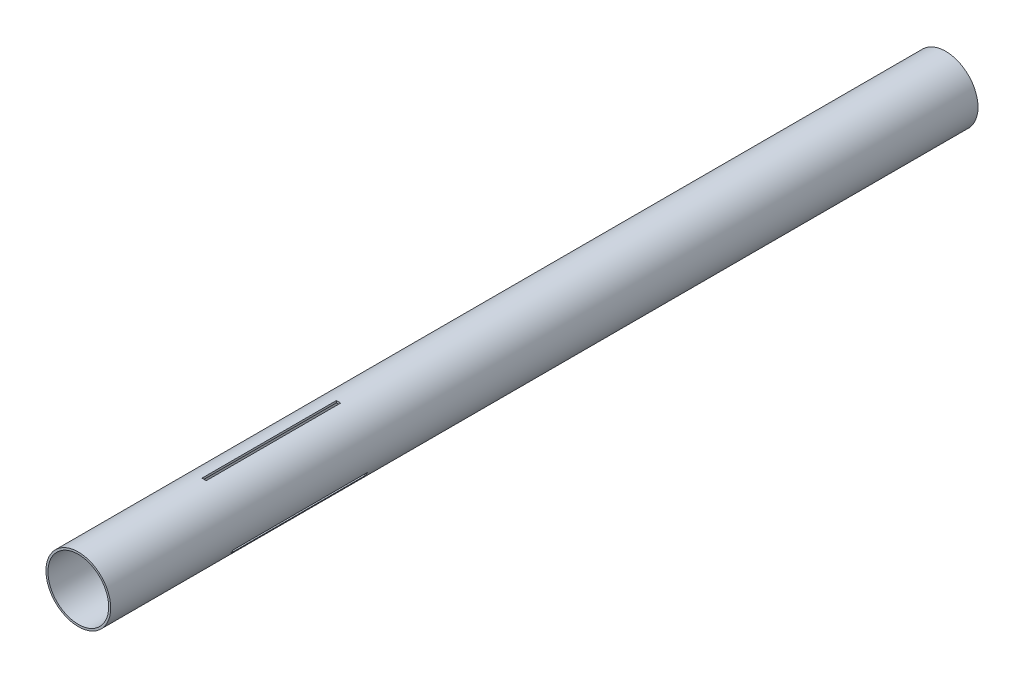
SolidWorks part; units mm, degrees
ref_plane "Front Plane" through (0, 0, 0) normal (0, 0, 1) x (1, 0, 0)
ref_plane "Top Plane" through (0, 0, 0) normal (0, 1, 0) x (1, 0, 0)
ref_plane "Right Plane" through (0, 0, 0) normal (1, 0, 0) x (0, 0, -1)
sketch "Sketch1" plane through (0, 0, 0) normal (0, 0, 1) x (1, 0, 0)
  circle A0 centre (0, 0) radius 23.6982
  circle A1 centre (0, 0) radius 22.225
  dimension "D1" = 47.3964
  dimension "D2" = 44.45
extrude "Boss-Extrude1" add sketch "Sketch1" along normal blind 635
ref_plane "Plane1" through (0, 100, 0) normal (0, 1, 0) x (1, 0, 0)
sketch "Sketch2" plane through (0, 100, 0) normal (0, 1, 0) x (1, 0, 0)
  line L3 (1.5875, -542.925) -> (1.5875, -444.5)
  line L4 (-1.5875, -542.925) -> (-1.5875, -444.5)
  line L5 (-1.5875, -444.5) -> (1.5875, -444.5)
  line L6 (-1.5875, -542.925) -> (1.5875, -542.925)
extrude "Cut-Extrude1" cut sketch "Sketch2" against normal up to next
pattern_circular "CirPattern2" count 3 over 360 about axis through (0, 0, 0) along (0, 0, 1) of "Cut-Extrude1"
